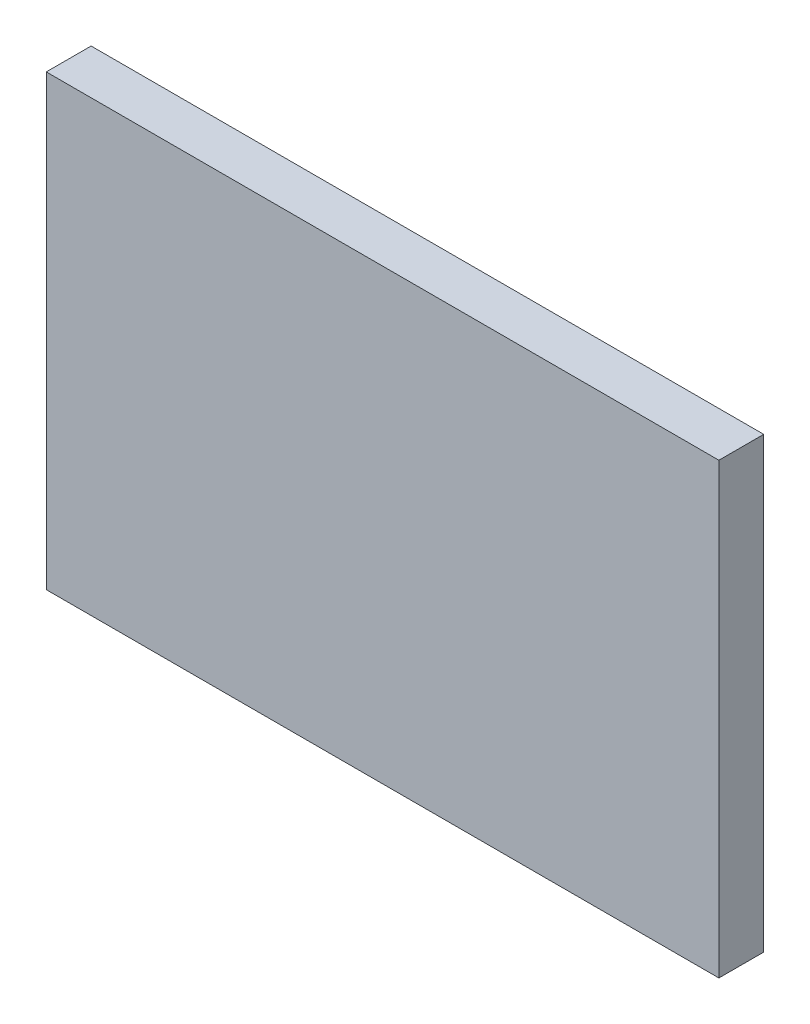
SolidWorks part; units mm, degrees
ref_plane "Plano frontal" through (0, 0, 0) normal (0, 0, 1) x (1, 0, 0)
ref_plane "Plano superior" through (0, 0, 0) normal (0, 1, 0) x (1, 0, 0)
ref_plane "Plano direito" through (0, 0, 0) normal (1, 0, 0) x (0, 0, -1)
sketch "Esboço1" plane through (0, 0, 0) normal (0, 0, 1) x (1, 0, 0)
  line L1 (-151.7572, -48.8669) -> (148.2428, -48.8669)
  line L2 (-151.7572, -48.8669) -> (-151.7572, 151.1331)
  line L3 (-151.7572, 151.1331) -> (148.2428, 151.1331)
  line L4 (148.2428, -48.8669) -> (148.2428, 151.1331)
  dimension "D1" = 300
  dimension "D2" = 200
extrude "Ressalto-extrusão1" add sketch "Esboço1" along normal blind 20
